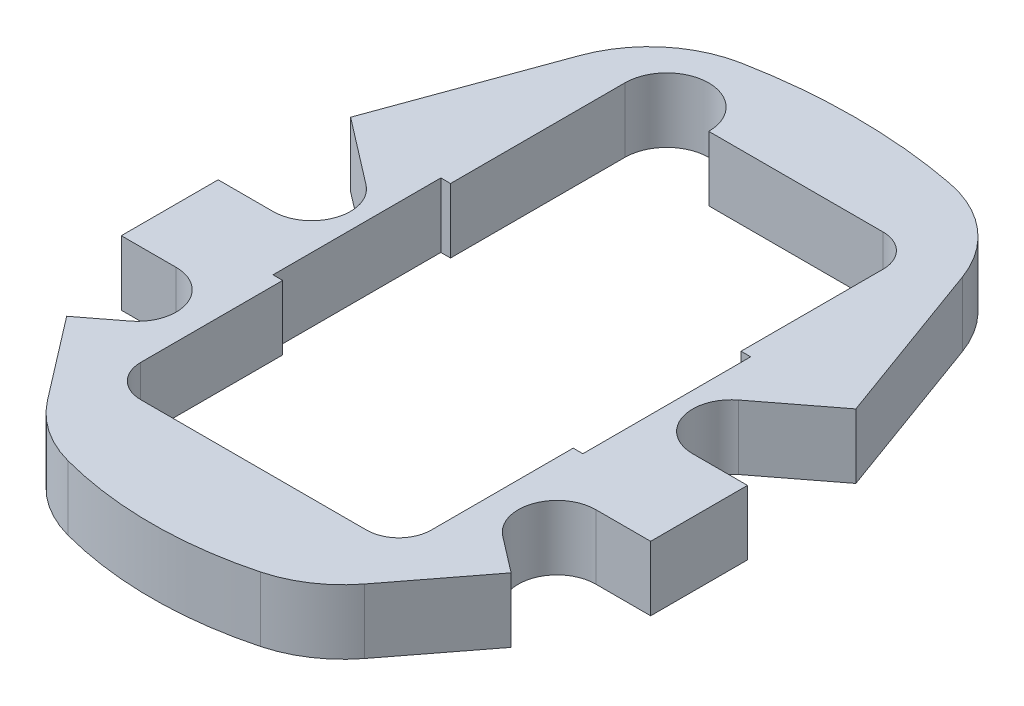
SolidWorks part; units mm, degrees
ref_plane "Plan de face" through (0, 0, 0) normal (0, 0, 1) x (1, 0, 0)
ref_plane "Plan de dessus" through (0, 0, 0) normal (0, 1, 0) x (1, 0, 0)
ref_plane "Plan de droite" through (0, 0, 0) normal (1, 0, 0) x (0, 0, -1)
sketch "Esquisse1" plane through (0, 0, 0) normal (0, 1, 0) x (1, 0, 0)
  line L0 (0, 66.2392) -> (0, -66.6254) construction
  line L1 (29.6684, 42.1628) -> (41, 11.0295)
  line L2 (41, 11.0295) -> (41, -23.9705)
  line L3 (41, -23.9705) -> (24.5634, -45.3911)
  line L4 (-41, -23.9705) -> (-24.5634, -45.3911)
  line L5 (-41, 11.0295) -> (-41, -23.9705)
  line L6 (-29.6684, 42.1628) -> (-41, 11.0295)
  line L7 (-22.5, -11) -> (-22.5, -33)
  line L8 (-9.5, 42) -> (17.5, 42)
  line L9 (-22.5, 42) -> (-22.5, 15)
  line L10 (-17.5, -38) -> (17.5, -38)
  line L11 (22.5, 37) -> (22.5, 15)
  line L12 (-24, 15) -> (-22.5, 15)
  line L13 (-24, 15) -> (-24, -11)
  line L14 (-24, -11) -> (-22.5, -11)
  line L15 (24, 15) -> (24, -11)
  line L16 (22.5, 15) -> (24, 15)
  line L17 (22.5, -11) -> (22.5, -33)
  line L18 (22.5, -11) -> (24, -11)
  arc A0 (16.155, 53.6822) -> (-16.155, 53.6822) centre (0, -30.2777) ccw
  arc A1 (-14.9105, -51.8284) -> (14.9105, -51.8284) centre (0, 4.2223) ccw
  arc A2 (16.155, 53.6822) -> (29.6684, 42.1628) centre (12.7539, 36.0064) cw
  arc A3 (24.5634, -45.3911) -> (14.9105, -51.8284) centre (10.2831, -34.4334) cw
  arc A4 (-24.5634, -45.3911) -> (-14.9105, -51.8284) centre (-10.2831, -34.4334) ccw
  arc A5 (-16.155, 53.6822) -> (-29.6684, 42.1628) centre (-12.7539, 36.0064) ccw
  arc A6 (-17.5, -38) -> (-22.5, -33) centre (-17.5, -33) cw
  arc A7 (22.5, -33) -> (17.5, -38) centre (17.5, -33) cw
  arc A8 (17.5, 42) -> (22.5, 37) centre (17.5, 37) cw
  arc A9 (-22.5, 42) -> (-9.5, 42) centre (-16, 42) cw
  point P30 (22.5, -38)
  point P33 (22.5, 42)
  dimension "D1" = 171
  dimension "D2" = 58
  dimension "D9" = 18
  dimension "D14" = 5
  dimension "D15" = 6.5
  dimension "D3" = 34.5
  dimension "D4" = 27
  dimension "D5" = 41
  dimension "D6" = 37.5
  dimension "D7" = 20
  dimension "D8" = 35
  dimension "D10" = 80
  dimension "D11" = 45
  dimension "D12" = 22.5
  dimension "D13" = 38
  dimension "D16" = 48
  dimension "D17" = 24
  dimension "D18" = 27
  dimension "D19" = 26
extrude "Extrusion1" add sketch "Esquisse1" along normal blind 10
sketch "Esquisse2" plane through (0, 10, 0) normal (0, 1, 0) x (-1, 0, 0)
  line L0 (44.2607, 10) -> (-47.9722, 10) construction
  line L1 (-44.2907, 17.5) -> (-32.5, 17.5)
  line L2 (-39.6539, 36.5522) -> (-28.8474, 28.2601)
  line L3 (-39.6539, 36.5522) -> (-44.2907, 29.7455)
  line L4 (-44.2907, 29.7455) -> (-44.2907, 17.5)
  line L5 (-41, 23.9705) -> (-41, -11.0295) construction
  line L6 (-24.5634, 45.3911) -> (-41, 23.9705) construction
  line L7 (-44.2907, -9.7455) -> (-44.2907, 2.5)
  line L8 (-39.6539, -16.5522) -> (-44.2907, -9.7455)
  line L9 (-39.6539, -16.5522) -> (-28.8474, -8.2601)
  line L10 (-44.2907, 2.5) -> (-32.5, 2.5)
  line L11 (0, -23.1089) -> (0, 59.0948) construction
  line L12 (-44.2607, 10) -> (47.9722, 10) construction
  line L13 (44.2907, 2.5) -> (32.5, 2.5)
  line L14 (39.6539, -16.5522) -> (28.8474, -8.2601)
  line L15 (39.6539, -16.5522) -> (44.2907, -9.7455)
  line L16 (44.2907, -9.7455) -> (44.2907, 2.5)
  line L17 (44.2907, 29.7455) -> (44.2907, 17.5)
  line L18 (39.6539, 36.5522) -> (44.2907, 29.7455)
  line L19 (39.6539, 36.5522) -> (28.8474, 28.2601)
  line L20 (44.2907, 17.5) -> (32.5, 17.5)
  arc A0 (-32.5, 17.5) -> (-28.8474, 28.2601) centre (-32.5, 23.5) ccw
  arc A1 (-32.5, 2.5) -> (-28.8474, -8.2601) centre (-32.5, -3.5) cw
  arc A2 (32.5, 2.5) -> (28.8474, -8.2601) centre (32.5, -3.5) ccw
  arc A3 (32.5, 17.5) -> (28.8474, 28.2601) centre (32.5, 23.5) cw
  dimension "D2" = 6
  dimension "D1" = 10
  dimension "D3" = 7.5
  dimension "D4" = 8.5
extrude "Extrusion3" cut sketch "Esquisse2" against normal blind 10
